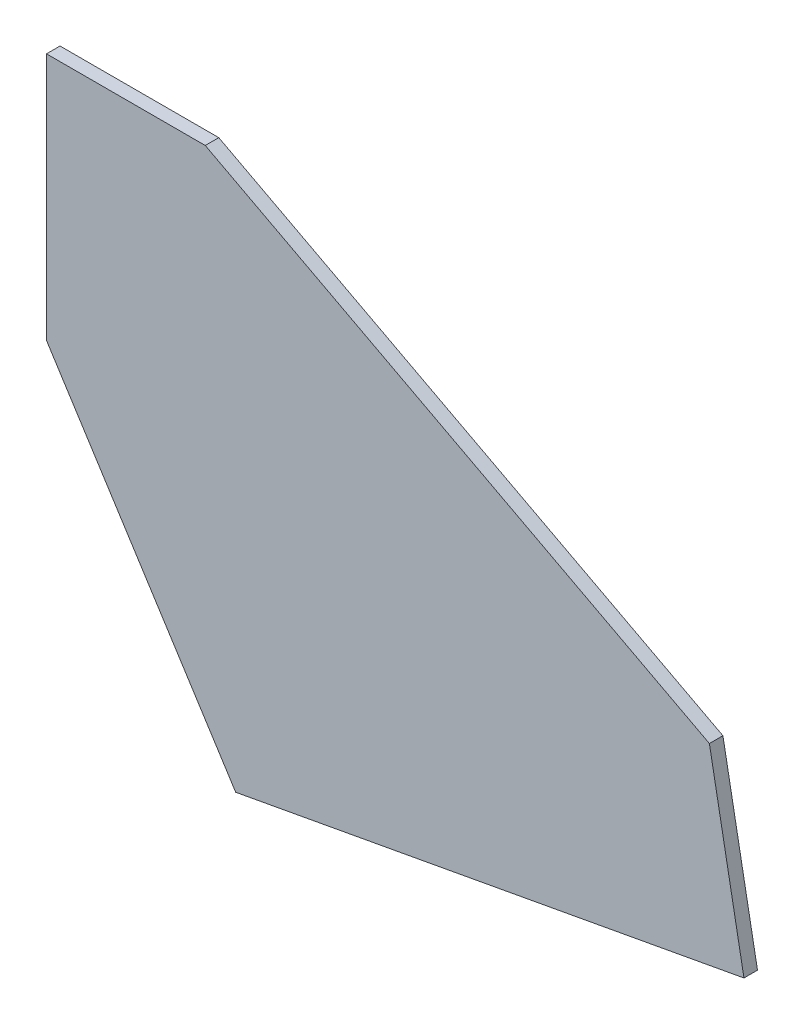
SolidWorks part; units mm, degrees
ref_plane "Front Plane" through (0, 0, 0) normal (0, 0, 1) x (1, 0, 0)
ref_plane "Top Plane" through (0, 0, 0) normal (0, 1, 0) x (1, 0, 0)
ref_plane "Right Plane" through (0, 0, 0) normal (1, 0, 0) x (0, 0, -1)
sketch "Sketch2" plane through (0, 0, 0) normal (0, 0, 1) x (1, 0, 0)
  line L1 (674.0303, -1015.6627) -> (817.0917, -989.4078)
  line L2 (817.0917, -989.4078) -> (807.3606, -937.1164)
  line L3 (807.3606, -937.1164) -> (665.4698, -862.2909)
  line L4 (665.4698, -862.2909) -> (620.7858, -862.2909)
  line L5 (620.7858, -862.2909) -> (620.7858, -932.1566)
  line L6 (620.7858, -932.1566) -> (674.0303, -1015.6627)
extrude "Boss-Extrude1" add sketch "Sketch2" along normal blind 3.81
